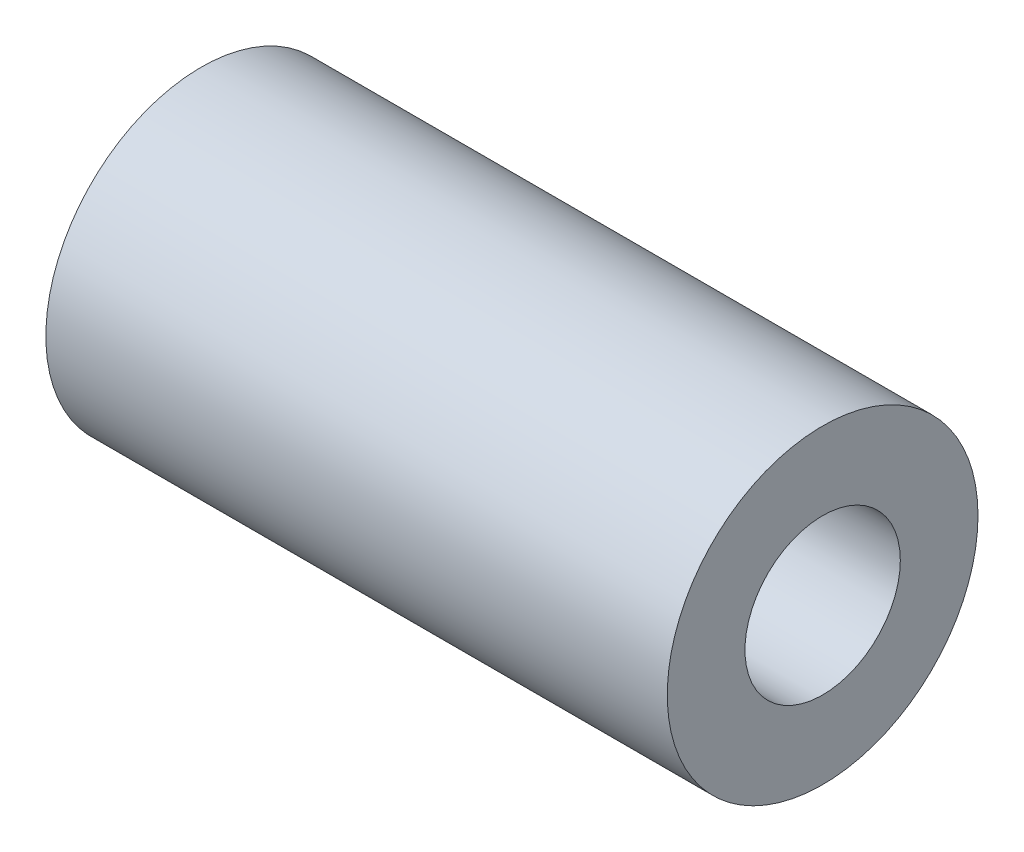
SolidWorks part; units mm, degrees
material "6063-T6"
ref_plane "Front Plane" through (0, 0, 0) normal (0, 0, 1) x (1, 0, 0)
ref_plane "Top Plane" through (0, 0, 0) normal (0, 1, 0) x (1, 0, 0)
ref_plane "Right Plane" through (0, 0, 0) normal (1, 0, 0) x (0, 0, -1)
sketch "Sketch1" plane through (0, 0, 0) normal (1, 0, 0) x (0, 0, -1)
  circle A0 centre (0, 0) radius 2.5
  circle A1 centre (0, 0) radius 5
  dimension "D1" = 5
  dimension "D2" = 10
extrude "Boss-Extrude1" add sketch "Sketch1" along normal blind 20
